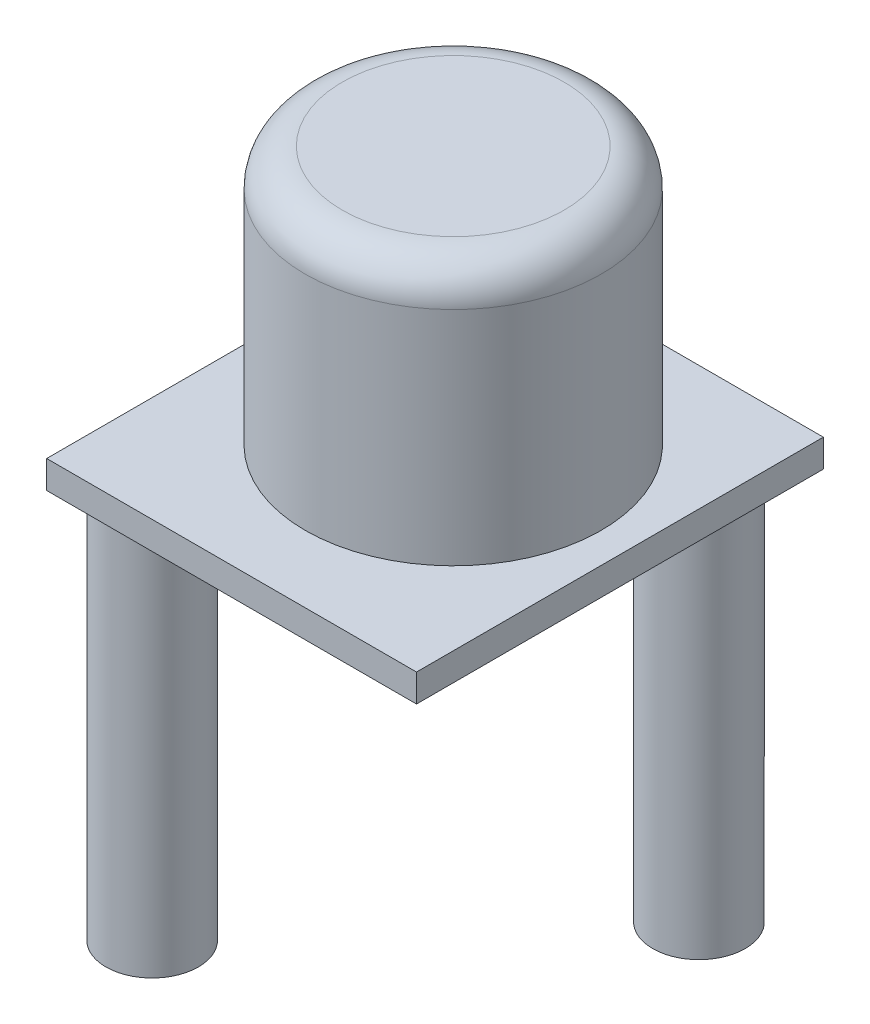
SolidWorks part; units mm, degrees
ref_plane "Frontal" through (0, 0, 0) normal (0, 0, 1) x (1, 0, 0)
ref_plane "Superior" through (0, 0, 0) normal (0, 1, 0) x (1, 0, 0)
ref_plane "Direito" through (0, 0, 0) normal (1, 0, 0) x (0, 0, -1)
sketch "Esboço1" plane through (0, 0, 0) normal (0, 1, 0) x (1, 0, 0)
  line L1 (-10.363, 8.7929) -> (9.637, 8.7929)
  line L2 (-10.363, 8.7929) -> (-10.363, -13.2071)
  line L3 (-10.363, -13.2071) -> (9.637, -13.2071)
  line L4 (9.637, 8.7929) -> (9.637, -13.2071)
  dimension "D1" = 22
  dimension "D2" = 20
extrude "Ressalto-extrusão1" add sketch "Esboço1" along normal blind 1.5
sketch "Esboço2" plane through (0, 1.5, 0) normal (0, 1, 0) x (1, 0, 0)
  circle A0 centre (0, -1.5848) radius 8
  dimension "D1" = 16
extrude "Ressalto-extrusão2" add sketch "Esboço2" along normal blind 14
fillet "Filete1" radius 2 1 edges at (0, 15.5, 9.5848)
sketch "Esboço3" plane through (0, 0, 0) normal (0, -1, 0) x (-1, 0, 0)
  circle A0 centre (7.4461, -10.4205) radius 2.5
  circle A1 centre (-6.4792, 5.2243) radius 2.5
  dimension "D1" = 5
  dimension "D2" = 5
extrude "Ressalto-extrusão3" add sketch "Esboço3" along normal blind 21
sketch "Esboço4" plane through (0, 0, 0) normal (0, -1, 0) x (-1, 0, 0)
  line L0 (10.363, 8.7929) -> (10.363, -13.2071) construction
  line L1 (8.363, 4.7929) -> (0.363, 4.7929)
  line L2 (8.363, 4.7929) -> (8.363, -3.2071)
  line L3 (8.363, -3.2071) -> (0.363, -3.2071)
  line L4 (0.363, 4.7929) -> (0.363, -3.2071)
  line L5 (-9.637, 8.7929) -> (10.363, 8.7929) construction
  dimension "D1" = 8
  dimension "D2" = 8
  dimension "D3" = 2
  dimension "D4" = 4
extrude "Ressalto-extrusão4" add sketch "Esboço4" along normal blind 10
